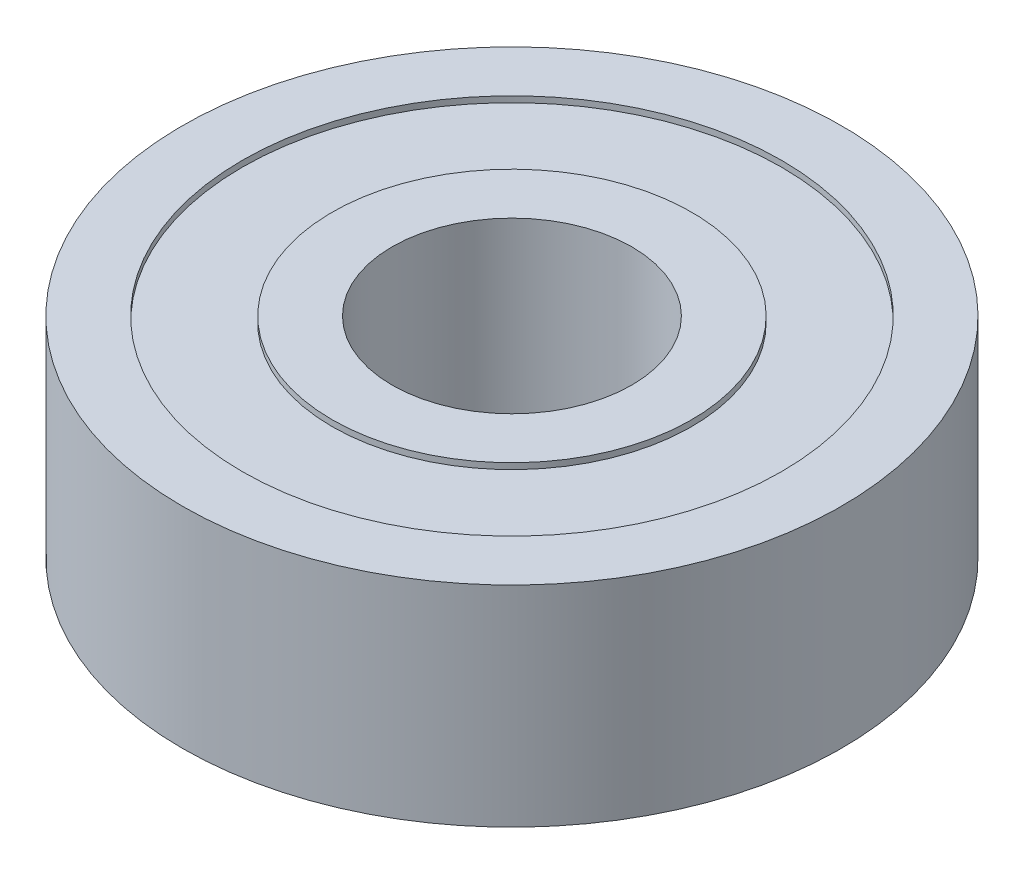
SolidWorks part; units mm, degrees
ref_plane "前视基准面" through (0, 0, 0) normal (0, 0, 1) x (1, 0, 0)
ref_plane "上视基准面" through (0, 0, 0) normal (0, 1, 0) x (1, 0, 0)
ref_plane "右视基准面" through (0, 0, 0) normal (1, 0, 0) x (0, 0, -1)
other "Configuration Table"
sketch "草图1" plane through (0, 0, 0) normal (0, 0, 1) x (1, 0, 0)
  line L0 (0, 19.3457) -> (0, -22.9805) construction
  line L1 (-4, 0) -> (-6, 0)
  line L2 (-11, 0) -> (-11, 7)
  line L3 (-11, 7) -> (-9, 7)
  line L4 (-4, 7) -> (-4, 0)
  line L5 (-9, 7) -> (-9, 6.8)
  line L6 (-9, 6.8) -> (-6, 6.8)
  line L7 (-6, 6.8) -> (-6, 7)
  line L8 (-6, 0) -> (-6, 0.2)
  line L9 (-6, 0.2) -> (-9, 0.2)
  line L10 (-9, 0.2) -> (-9, 0)
  line L11 (-6, 7) -> (-4, 7)
  line L12 (-9, 0) -> (-11, 0)
  dimension "D1" = 11
  dimension "D2" = 4
  dimension "D3" = 7
  dimension "D4" = 0.2
  dimension "D5" = 0.2
  dimension "D6" = 2
  dimension "D7" = 2
revolve "旋转1" add sketch "草图1" angle 360 about L0
